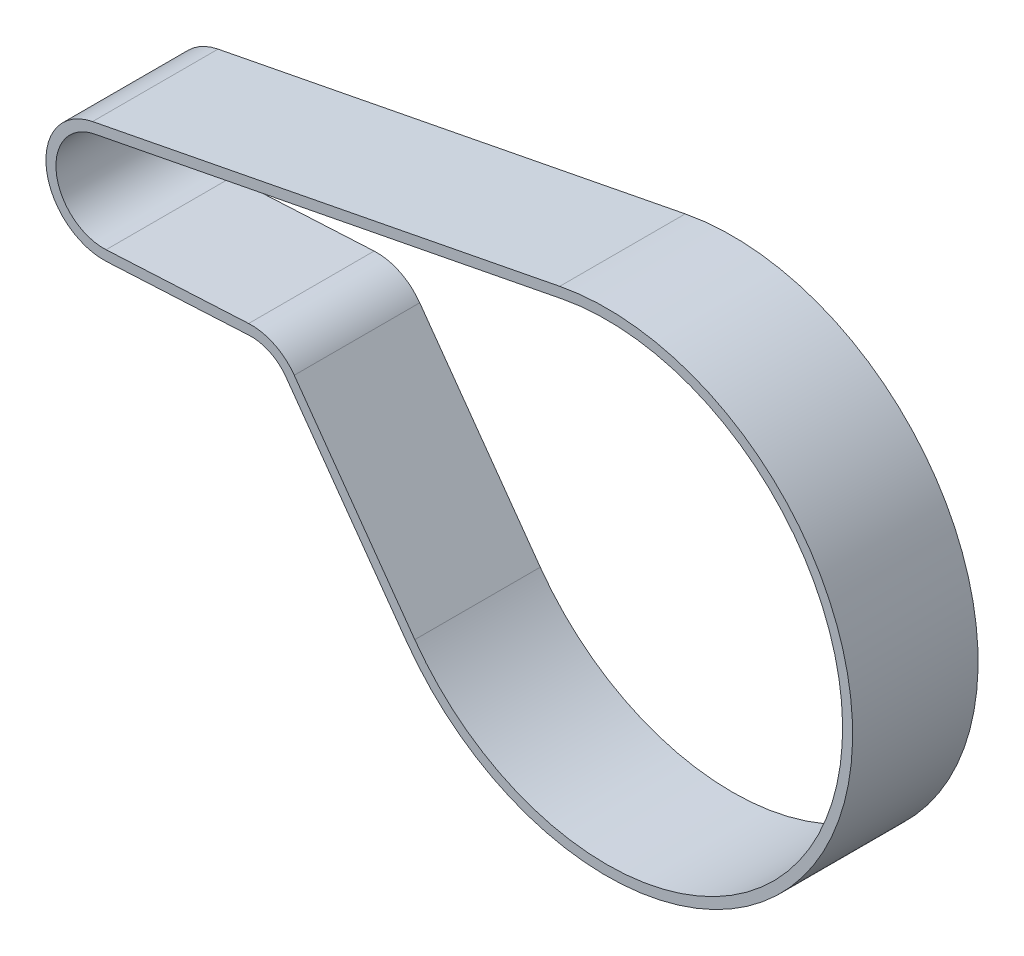
SolidWorks part; units mm, degrees
ref_plane "Ön Düzlem" through (0, 0, 0) normal (0, 0, 1) x (1, 0, 0)
ref_plane "Üst Düzlem" through (0, 0, 0) normal (0, 1, 0) x (1, 0, 0)
ref_plane "Sağ Düzlem" through (0, 0, 0) normal (1, 0, 0) x (0, 0, -1)
sketch "Sketch2" plane through (0, 0, 0) normal (0, 0, 1) x (1, 0, 0)
  line L0 (0, 0) -> (1, 0) construction
  line L1 (0, 0) -> (0, 1) construction
  line L2 (-1.8142, 9.3252) -> (91.2747, 27.4351)
  line L6 (62.0045, -46.0182) -> (37.9894, -12.397)
  line L7 (28.9015, -8.0141) -> (0.492, -9.4873)
  arc A0 (0.492, -9.4873) -> (-1.8142, 9.3252) centre (0, 0) cw
  arc A1 (91.2747, 27.4351) -> (62.0045, -46.0182) centre (100.25, -18.7) cw
  arc A3 (37.9894, -12.397) -> (28.9015, -8.0141) centre (29.4452, -18.5) ccw
extrude "Extrude-Thin1" add sketch "Sketch2" along normal blind 15.5 and the other way blind 9.5 thin thin type one direction wall 2
